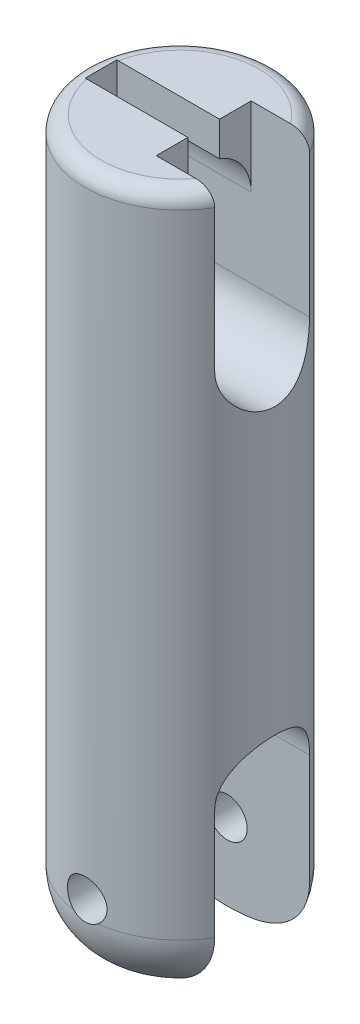
SolidWorks part; units mm, degrees
material "1.0037 (S235JR)"
ref_plane "Front Plane" through (0, 0, 0) normal (0, 0, 1) x (1, 0, 0)
ref_plane "Top Plane" through (0, 0, 0) normal (0, 1, 0) x (1, 0, 0)
ref_plane "Right Plane" through (0, 0, 0) normal (1, 0, 0) x (0, 0, -1)
sketch "Sketch1" plane through (0, 0, 0) normal (0, 1, 0) x (1, 0, 0)
  circle A0 centre (0, 0) radius 6
  dimension "D1" = 12
extrude "Boss-Extrude1" add sketch "Sketch1" along normal blind 45
fillet "Fillet1" radius 1 1 edges at (0, 45, 6)
fillet "Fillet2" radius 4 1 edges at (0, 0, 6)
sketch "Sketch2" plane through (0, 0, 0) normal (0, 0, 1) x (1, 0, 0)
  line L0 (-2, 0) -> (2, 0) construction
  circle A0 centre (0, 5) radius 1.25
  dimension "D1" = 2.5
  dimension "D2" = 5
extrude "Cut-Extrude1" cut sketch "Sketch2" against normal through all both and the other way through all
sketch "Sketch3" plane through (0, 0, 0) normal (1, 0, 0) x (0, 0, -1)
  line L1 (0, 0) -> (0, 11) construction
  line L2 (-3, 0) -> (-3, 11)
  line L3 (3, 0) -> (3, 11)
  arc A0 (-3, 0) -> (3, 0) centre (0, 0) ccw
  arc A1 (3, 11) -> (-3, 11) centre (0, 11) ccw
  point P2 (0, 5.5)
  dimension "D1" = 6
  dimension "D2" = 11
extrude "Cut-Extrude2" cut sketch "Sketch3" against normal through all both and the other way through all
sketch "Sketch4" plane through (0, 0, 0) normal (1, 0, 0) x (0, 0, -1)
  line L0 (0, 35) -> (0, 40) construction
  line L1 (-3, 35) -> (-3, 40)
  line L2 (3, 35) -> (3, 40)
  line L3 (3, 11) -> (3, 4) construction
  line L5 (5, 45) -> (-5, 45) construction
  arc A0 (-3, 35) -> (3, 35) centre (0, 35) ccw
  arc A1 (3, 40) -> (-3, 40) centre (0, 40) ccw
  point P3 (0, 37.5)
  dimension "D1" = 5
  dimension "D2" = 10
extrude "Cut-Extrude3" cut sketch "Sketch4" against normal blind 5 and the other way through all
sketch "Sketch5" plane through (0, 0, 0) normal (1, 0, 0) x (0, 0, -1)
  line L0 (0, 45) -> (0, 40) construction
  line L1 (5, 45) -> (-5, 45) construction
  line L2 (1, 45) -> (1, 40)
  line L3 (-1, 45) -> (-1, 40)
  arc A0 (1, 45) -> (-1, 45) centre (0, 45) ccw
  arc A1 (-1, 40) -> (1, 40) centre (0, 40) ccw
  point P5 (0, 42.5)
  dimension "D1" = 1
extrude "Cut-Extrude4" cut sketch "Sketch5" against normal blind 5 and the other way through all
ref_plane "Plane1" through (1.5, 0, 0) normal (1, 0, 0) x (0, 0, -1)
sketch "Sketch6" plane through (1.5, 0, 0) normal (1, 0, 0) x (0, 0, -1)
  line L0 (0, 45) -> (0, 36.7724) construction
  line L1 (3, 45) -> (3, 36.7724)
  line L2 (-3, 45) -> (-3, 36.7724)
  line L3 (3, 35) -> (3, 40) construction
  arc A0 (3, 45) -> (-3, 45) centre (0, 45) ccw
  arc A1 (-3, 36.7724) -> (3, 36.7724) centre (0, 36.7724) ccw
  spline S0 degree 3 poles (-1, 44.9951) (-0.6678, 45.0016) (-0.3354, 45) (0.3292, 45) (0.6658, 45.0016) (1, 44.9951) knots 0 0 0 0 0.5 0.5 1 1 1 1 construction
  point P5 (0, 40.8862)
extrude "Cut-Extrude5" cut sketch "Sketch6" along normal blind 10
